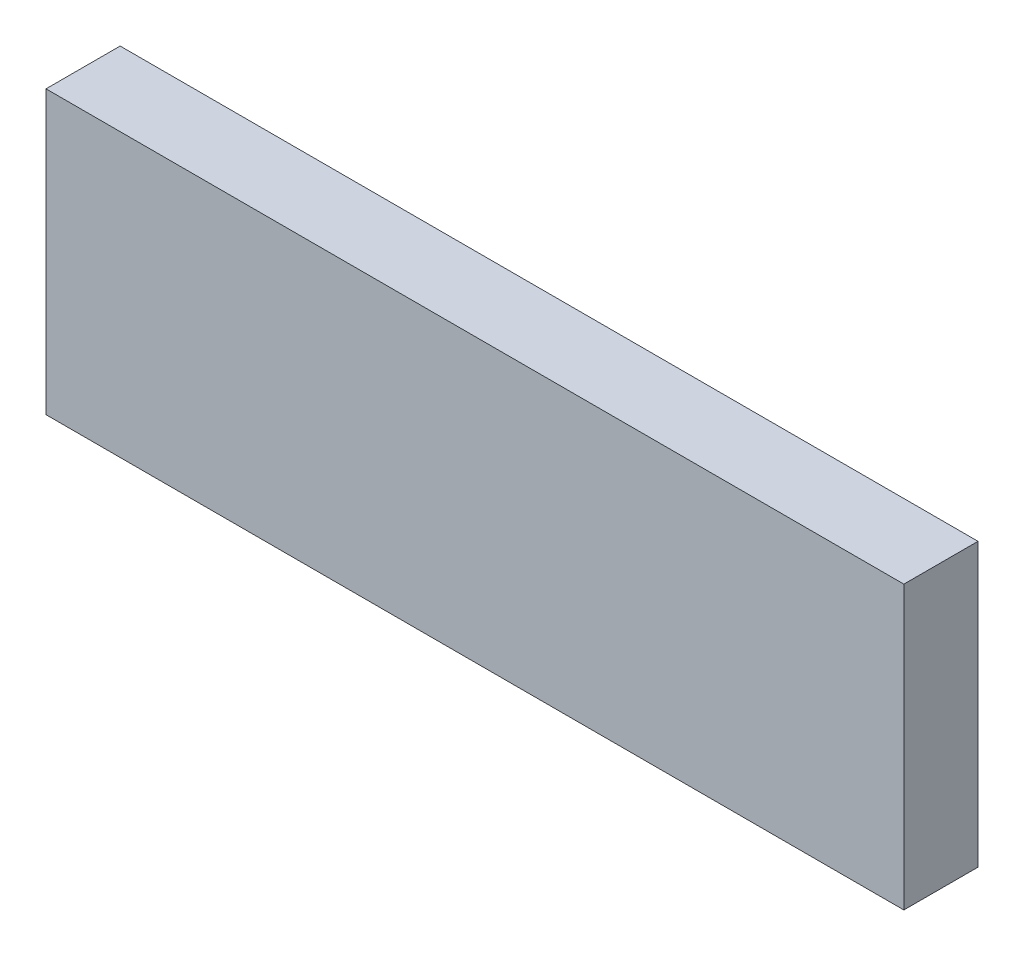
SolidWorks part; units mm, degrees
ref_plane "Front Plane" through (0, 0, 0) normal (0, 0, 1) x (1, 0, 0)
ref_plane "Top Plane" through (0, 0, 0) normal (0, 1, 0) x (1, 0, 0)
ref_plane "Right Plane" through (0, 0, 0) normal (1, 0, 0) x (0, 0, -1)
sketch "Sketch1" plane through (0, 0, 0) normal (0, 0, 1) x (1, 0, 0)
  line L1 (-112.34, 36.957) -> (112.34, 36.957)
  line L2 (-112.34, 36.957) -> (-112.34, -36.957)
  line L3 (-112.34, 0) -> (-72.4919, 0) construction
  line L4 (112.34, 36.957) -> (112.34, -36.957)
  line L5 (-112.34, 35.7) -> (-112.34, -35.7) construction
  line L6 (112.34, -35.7) -> (112.34, 35.7) construction
  line L7 (-112.34, -36.957) -> (112.34, -36.957)
  line L8 (83.82, 38.227) -> (93.98, 38.227) construction
  point P14 (112.34, 0)
  dimension "D1" = 1.27
extrude "Boss-Extrude1" add sketch "Sketch1" along normal offset from surface (19.419 mm away) 2.54
